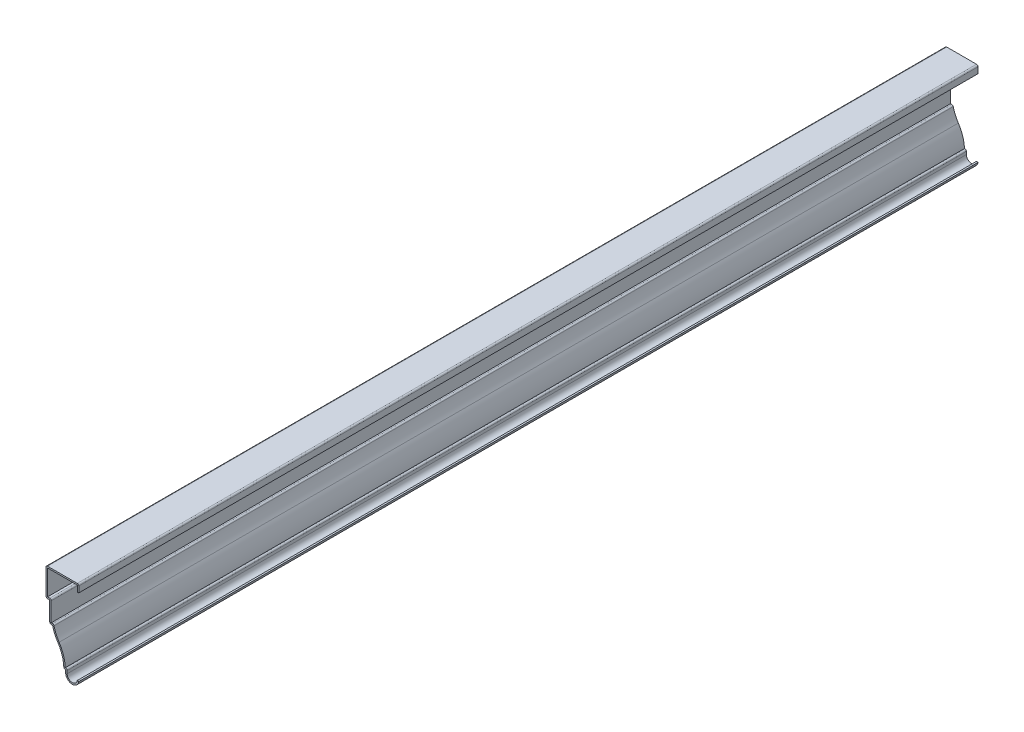
SolidWorks part; units mm, degrees
ref_plane "Front Plane" through (0, 0, 0) normal (0, 0, 1) x (1, 0, 0)
ref_plane "Top Plane" through (0, 0, 0) normal (0, 1, 0) x (1, 0, 0)
ref_plane "Right Plane" through (0, 0, 0) normal (1, 0, 0) x (0, 0, -1)
sketch "Sketch1" plane through (0, 0, 0) normal (0, 0, 1) x (1, 0, 0)
  line L0 (0, 0) -> (0, 76.2) construction
  line L1 (0, 0) -> (-41.6943, 0) construction
  line L2 (-11.1125, 5.5868) -> (-11.1125, 7.9375)
  line L3 (-11.1125, 7.9375) -> (-12.7, 7.9375)
  line L4 (-22.225, 34.925) -> (-24.6062, 34.925)
  line L5 (-24.6062, 34.925) -> (-24.6062, 52.3875)
  line L6 (-24.6062, 52.3875) -> (-27.7812, 52.3875)
  line L7 (-27.7812, 52.3875) -> (-27.7812, 76.2)
  line L8 (-27.7812, 76.2) -> (0, 76.2)
  line L9 (0, 76.2) -> (0, 69.85)
  arc A0 (0, 4.7625) -> (-11.1125, 5.5868) centre (-5.5257, 5.5868) cw
  arc A1 (-12.7, 7.9375) -> (-17.7209, 24.6011) centre (-42.8625, 7.9375) ccw
  arc A2 (-17.7209, 24.6011) -> (-22.225, 34.925) centre (9.4056, 42.5803) cw
  point P13 (-17.8936, 25.678)
  point P18 (0, 75.3444)
  dimension "D12" = 30.1625
  dimension "D13" = 32.5437
  dimension "D1" = 76.2
  dimension "D2" = 11.1125
  dimension "D3" = 4.7625
  dimension "D4" = 23.8125
  dimension "D5" = 17.4625
  dimension "D6" = 27.7812
  dimension "D7" = 3.175
  dimension "D8" = 2.3813
  dimension "D9" = 1.5875
  dimension "D10" = 65.0875
  dimension "D11" = 6.35
  dimension "D14" = 7.9375
extrude "Extrude-Thin1" add sketch "Sketch1" against normal blind 762 thin
fillet "Fillet1" radius 1.27 8 edges at (-9.8425, 9.2075, -381) (-12.7, 7.9375, -381) (-21.2094, 36.195, -381) (-24.6062, 34.925, -381) (-23.3362, 53.6575, -381) (-27.7812, 52.3875, -381) (-27.7812, 76.2, -381) (0, 76.2, -381)
